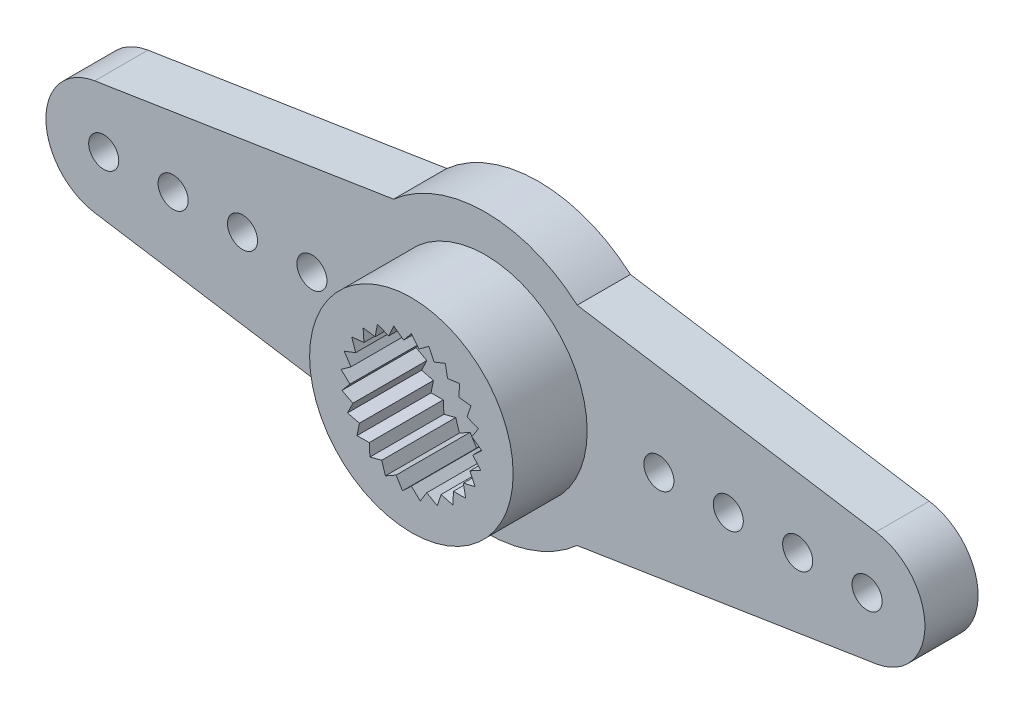
SolidWorks part; units mm, degrees
ref_plane "Front" through (0, 0, 0) normal (0, 0, 1) x (1, 0, 0)
ref_plane "Top" through (0, 0, 0) normal (0, 1, 0) x (1, 0, 0)
ref_plane "Right" through (0, 0, 0) normal (1, 0, 0) x (0, 0, -1)
sketch "Эскиз1" plane through (0, 0, 0) normal (0, 0, 1) x (1, 0, 0)
  line L0 (-3.9686, 4.5) -> (-16.8881, 2.4697)
  line L1 (-19, 4.5) -> (19, 4.5) construction
  line L2 (-19, 4.5) -> (-19, -4.5) construction
  line L3 (-19, -4.5) -> (19, -4.5) construction
  line L4 (19, 4.5) -> (19, -4.5) construction
  line L5 (0, -4.5) -> (0, 4.5) construction
  line L6 (-19, 0) -> (19, 0) construction
  line L7 (-3.9686, -4.5) -> (-16.8881, -2.4697)
  line L8 (3.9686, -4.5) -> (16.8881, -2.4697)
  line L9 (3.9686, 4.5) -> (16.8881, 2.4697)
  circle A0 centre (0, 0) radius 6 construction
  circle A1 centre (-16.5, 0) radius 2.5 construction
  arc A2 (-16.8881, 2.4697) -> (-16.8881, -2.4697) centre (-16.5, 0) ccw
  arc A3 (-3.9686, 4.5) -> (3.9686, 4.5) centre (0, 0) cw
  arc A4 (-3.9686, -4.5) -> (3.9686, -4.5) centre (0, 0) ccw
  circle A5 centre (16.5, 0) radius 2.5 construction
  arc A6 (16.8881, 2.4697) -> (16.8881, -2.4697) centre (16.5, 0) cw
  circle A7 centre (-16.5, 0) radius 0.65
  circle A8 centre (-13.5, 0) radius 0.65
  circle A9 centre (-10.5, 0) radius 0.65
  circle A10 centre (-7.5, 0) radius 0.65
  circle A11 centre (16.5, 0) radius 0.65
  circle A12 centre (7.5, 0) radius 0.65
  circle A13 centre (10.5, 0) radius 0.65
  circle A14 centre (13.5, 0) radius 0.65
  circle A15 centre (0, 0) radius 1.5
  dimension "D1" = 12
  dimension "D4" = 5
  dimension "D5" = 1.3
  dimension "D7" = 3
  dimension "D2" = 9
  dimension "D3" = 38
  dimension "D6" = 4
extrude "Бобышка-Вытянуть1" add sketch "Эскиз1" along normal blind 2.3
sketch "Эскиз2" plane through (0, 0, 2.3) normal (0, 0, 1) x (1, 0, 0)
  line L0 (0, 0) -> (0, 3.05) construction
  line L1 (0, 0) -> (0.3823, 3.0259) construction
  line L2 (0.3334, 2.6394) -> (0, 3.05)
  line L3 (-0.3334, 2.6394) -> (0, 3.05)
  line L4 (0.3334, 2.6394) -> (0.7585, 2.9542)
  line L5 (0.9794, 2.4736) -> (0.7585, 2.9542)
  line L6 (0.9794, 2.4736) -> (1.4693, 2.6727)
  line L7 (1.5638, 2.1523) -> (1.4693, 2.6727)
  line L8 (1.5638, 2.1523) -> (2.0879, 2.2234)
  line L9 (2.0499, 1.6958) -> (2.0879, 2.2234)
  line L10 (2.0499, 1.6958) -> (2.5752, 1.6343)
  line L11 (2.4072, 1.1328) -> (2.5752, 1.6343)
  line L12 (2.4072, 1.1328) -> (2.9007, 0.9425)
  line L13 (2.6133, 0.4985) -> (2.9007, 0.9425)
  line L14 (2.6133, 0.4985) -> (3.044, 0.1915)
  line L15 (2.6552, -0.167) -> (3.044, 0.1915)
  line L16 (2.6552, -0.167) -> (2.996, -0.5715)
  line L17 (2.5302, -0.8221) -> (2.996, -0.5715)
  line L18 (2.5302, -0.8221) -> (2.7597, -1.2986)
  line L19 (2.2463, -1.4255) -> (2.7597, -1.2986)
  line L20 (2.2463, -1.4255) -> (2.3501, -1.9441)
  line L21 (1.8212, -1.9394) -> (2.3501, -1.9441)
  line L22 (1.8212, -1.9394) -> (1.7927, -2.4675)
  line L23 (1.2817, -2.3313) -> (1.7927, -2.4675)
  line L24 (1.2817, -2.3313) -> (1.1228, -2.8358)
  line L25 (0.6616, -2.5768) -> (1.1228, -2.8358)
  line L26 (0.6616, -2.5768) -> (0.3823, -3.0259)
  line L27 (0, -2.6604) -> (0.3823, -3.0259)
  line L28 (0, -2.6604) -> (-0.3823, -3.0259)
  line L29 (-0.6616, -2.5768) -> (-0.3823, -3.0259)
  line L30 (-0.6616, -2.5768) -> (-1.1228, -2.8358)
  line L31 (-1.2817, -2.3313) -> (-1.1228, -2.8358)
  line L32 (-1.2817, -2.3313) -> (-1.7927, -2.4675)
  line L33 (-1.8212, -1.9394) -> (-1.7927, -2.4675)
  line L34 (-1.8212, -1.9394) -> (-2.3501, -1.9441)
  line L35 (-2.2463, -1.4255) -> (-2.3501, -1.9441)
  line L36 (-2.2463, -1.4255) -> (-2.7597, -1.2986)
  line L37 (-2.5302, -0.8221) -> (-2.7597, -1.2986)
  line L38 (-2.5302, -0.8221) -> (-2.996, -0.5715)
  line L39 (-2.6552, -0.167) -> (-2.996, -0.5715)
  line L40 (-2.6552, -0.167) -> (-3.044, 0.1915)
  line L41 (-2.6133, 0.4985) -> (-3.044, 0.1915)
  line L42 (-2.6133, 0.4985) -> (-2.9007, 0.9425)
  line L43 (-2.4072, 1.1328) -> (-2.9007, 0.9425)
  line L44 (-2.4072, 1.1328) -> (-2.5752, 1.6343)
  line L45 (-2.0499, 1.6958) -> (-2.5752, 1.6343)
  line L46 (-2.0499, 1.6958) -> (-2.0879, 2.2234)
  line L47 (-1.5638, 2.1523) -> (-2.0879, 2.2234)
  line L48 (-1.5638, 2.1523) -> (-1.4693, 2.6727)
  line L49 (-0.9794, 2.4736) -> (-1.4693, 2.6727)
  line L50 (-0.9794, 2.4736) -> (-0.7585, 2.9542)
  line L51 (-0.3334, 2.6394) -> (-0.7585, 2.9542)
  circle A0 centre (0, 0) radius 4.4
  circle A1 centre (0, 0) radius 3.05 construction
  circle A2 centre (0, 0) radius 2.65 construction
  point P83 (0, 0)
  dimension "D1" = 8.8
  dimension "D2" = 6.1
  dimension "D3" = 5.3
  dimension "D5" = 25
  dimension "D4" = 7.2
extrude "Бобышка-Вытянуть2" add sketch "Эскиз2" along normal blind 3.2
sketch "Эскиз3" plane through (0, 0, 0) normal (0, 0, -1) x (-1, 0, 0)
  circle A0 centre (0, 0) radius 4.4
  circle A1 centre (0, 0) radius 3.4
  circle A2 centre (0, 0) radius 2.75
  circle M17 centre (0, 0) radius 1.5
  dimension "D1" = 8.8
  dimension "D2" = 6.8
  dimension "D3" = 5.5
extrude "Вырез-Вытянуть1" cut sketch "Эскиз3" against normal blind 1 contours A0 A1 | A2 M17
